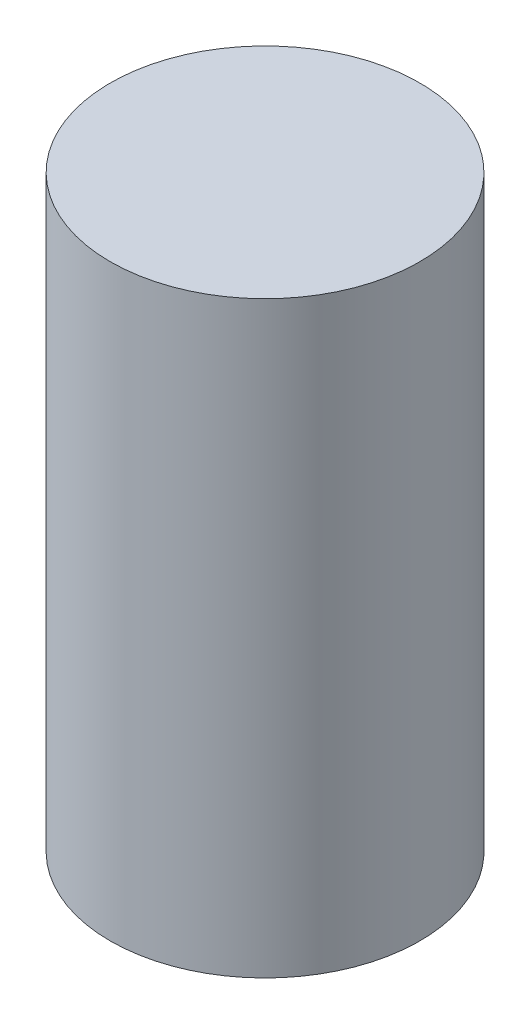
SolidWorks part; units mm, degrees
material "Chrome Stainless Steel"
ref_plane "Front Plane" through (0, 0, 0) normal (0, 0, 1) x (1, 0, 0)
ref_plane "Top Plane" through (0, 0, 0) normal (0, 1, 0) x (1, 0, 0)
ref_plane "Right Plane" through (0, 0, 0) normal (1, 0, 0) x (0, 0, -1)
sketch "Sketch1" plane through (0, 0, 0) normal (0, 1, 0) x (1, 0, 0)
  circle A0 centre (0, 0) radius 32.5
  dimension "D1" = 65
extrude "Boss-Extrude1" add sketch "Sketch1" along normal blind 123.5
